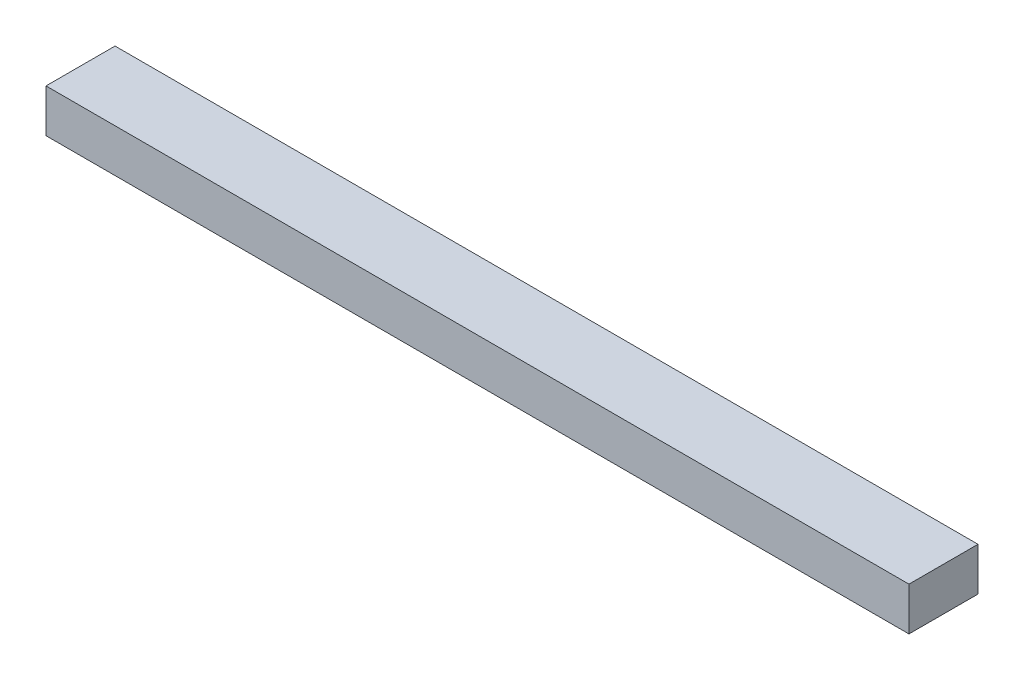
SolidWorks part; units mm, degrees
material "西洋杉"
ref_plane "正面" through (0, 0, 0) normal (0, 0, 1) x (1, 0, 0)
ref_plane "平面" through (0, 0, 0) normal (0, 1, 0) x (1, 0, 0)
ref_plane "右側面" through (0, 0, 0) normal (1, 0, 0) x (0, 0, -1)
sketch "ｽｹｯﾁ1" plane through (0, 0, 0) normal (0, 1, 0) x (1, 0, 0)
  line L1 (-500, 40) -> (500, 40)
  line L2 (-500, 40) -> (-500, -40)
  line L3 (-500, -40) -> (500, -40)
  line L4 (500, 40) -> (500, -40)
  line L5 (-500, 40) -> (500, -40) construction
  line L6 (-500, -40) -> (500, 40) construction
  point P0 (0, 0)
  dimension "D1" = 1000
  dimension "D2" = 80
extrude "ﾎﾞｽ - 押し出し1" add sketch "ｽｹｯﾁ1" along normal blind 50
